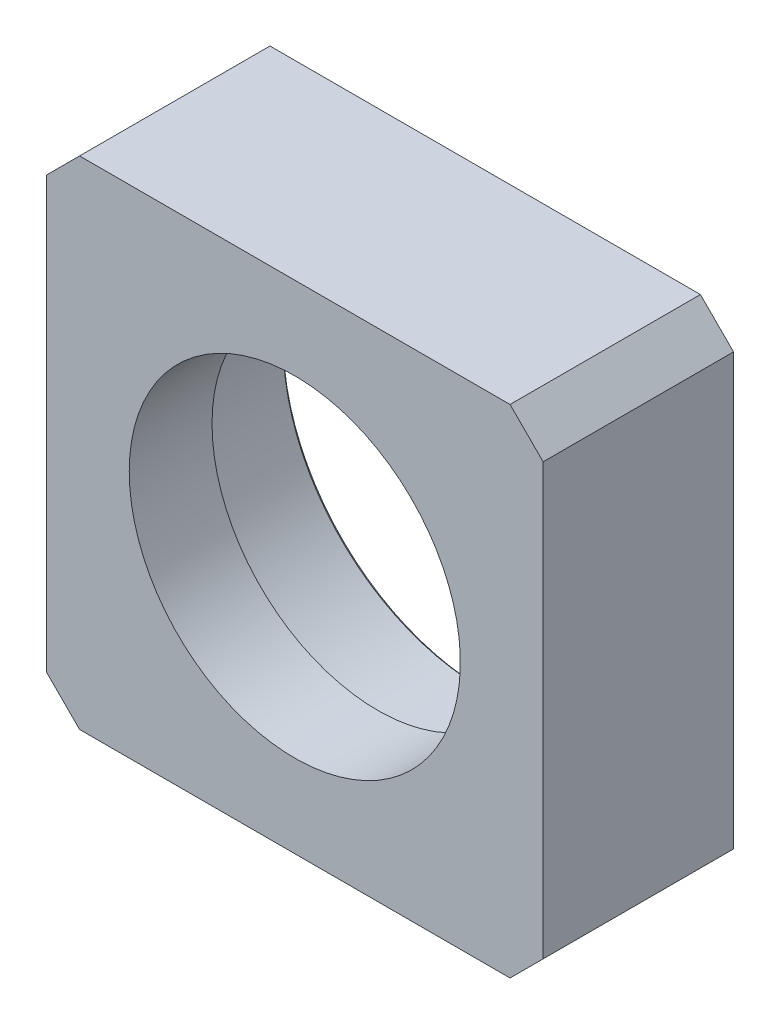
SolidWorks part; units mm, degrees
material "6061 合金"
ref_plane "前视基准面" through (0, 0, 0) normal (0, 0, 1) x (1, 0, 0)
ref_plane "上视基准面" through (0, 0, 0) normal (0, 1, 0) x (1, 0, 0)
ref_plane "右视基准面" through (0, 0, 0) normal (1, 0, 0) x (0, 0, -1)
sketch "Sketch1" plane through (0, 0, 0) normal (0, 0, 1) x (1, 0, 0)
  line L1 (-15, -15) -> (15, -15)
  line L2 (-15, -15) -> (-15, 15)
  line L3 (-15, 15) -> (15, 15)
  line L4 (15, -15) -> (15, 15)
  line L5 (-15, -15) -> (15, 15) construction
  line L6 (-15, 15) -> (15, -15) construction
  point P0 (0, 0)
  dimension "D1" = 30
  dimension "D2" = 30
extrude "Boss-Extrude1" add sketch "Sketch1" along normal blind 11.5 contours L4 L3 L2 L1
sketch "Sketch2" plane through (0, 0, 0) normal (0, 0, -1) x (-1, 0, 0)
  circle A0 centre (0, 0) radius 12
  dimension "D1" = 24
extrude "Cut-Extrude1" cut sketch "Sketch2" against normal blind 6.5
sketch "Sketch3" plane through (0, 0, 6.5) normal (0, 0, -1) x (-1, 0, 0)
  circle A0 centre (0, 0) radius 10
  dimension "D1" = 20
extrude "Cut-Extrude2" cut sketch "Sketch3" against normal through all contours A0
chamfer "Chamfer1" distance 2 angle 45 4 edges at (-15, -15, 5.75) (15, -15, 5.75) (-15, 15, 5.75) (15, 15, 5.75)
chamfer "倒角1" distance 0.2 angle 45 1 edges at (-12, 0, 0)
